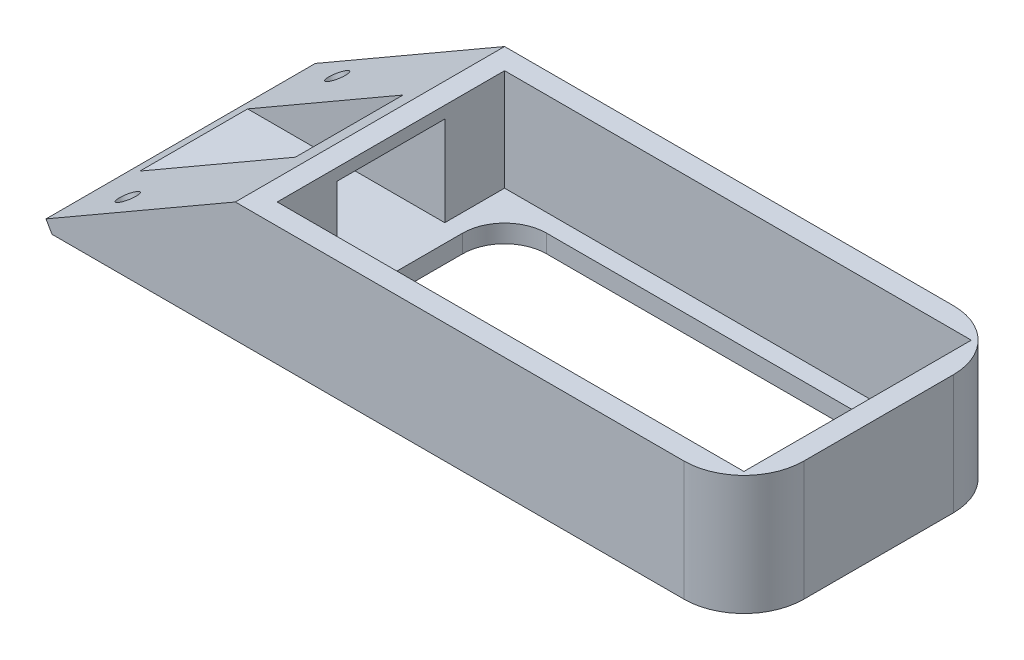
SolidWorks part; units mm, degrees
ref_plane "Front Plane" through (0, 0, 0) normal (0, 0, 1) x (1, 0, 0)
ref_plane "Top Plane" through (0, 0, 0) normal (0, 1, 0) x (1, 0, 0)
ref_plane "Right Plane" through (0, 0, 0) normal (1, 0, 0) x (0, 0, -1)
sketch "Sketch1" plane through (0, 0, 0) normal (0, 0, 1) x (1, 0, 0)
  line L0 (0, 0) -> (34.641, 20)
  line L1 (0, 0) -> (119.641, 0)
  line L2 (0, 0) -> (0, 20)
  line L3 (0, 20) -> (119.641, 20)
  line L4 (119.641, 0) -> (119.641, 20)
  line L5 (4, 0) -> (3, 1.7321)
  line L7 (34.641, 20) -> (34.641, 0) construction
  point P5 (5.8262, 0)
  point P10 (4.4285, 2.5568)
  dimension "D1" = 30
  dimension "D2" = 60
  dimension "D3" = 20
  dimension "D4" = 85
  dimension "D5" = 2
extrude "Boss-Extrude1" add sketch "Sketch1" along normal blind 45 contours L7 L0 L1 | L3 L7 L1 L4
sketch "Sketch2" plane through (0, 20, 0) normal (0, 1, 0) x (1, 0, 0)
  line L0 (116.141, -22.5) -> (119.641, -22.5) construction
  line L1 (38.141, -41.5) -> (116.141, -41.5)
  line L2 (38.141, -41.5) -> (38.141, -3.5)
  line L3 (38.141, -3.5) -> (116.141, -3.5)
  line L4 (116.141, -41.5) -> (116.141, -3.5)
  line L6 (119.641, -45) -> (119.641, 0) construction
  line L8 (77.141, -3.5) -> (77.141, 0) construction
  line L9 (34.641, 0) -> (119.641, 0) construction
  line L10 (38.141, -22.5) -> (34.641, -22.5) construction
  line L11 (34.641, -45) -> (34.641, 0) construction
  dimension "D1" = 78
  dimension "D2" = 38
extrude "Cut-Extrude1" cut sketch "Sketch2" against normal offset from surface (17 mm away) 3 up to face at (61.8205, 0, 22.5)
sketch "Sketch3" plane through (0, 3, 0) normal (0, 1, 0) x (1, 0, 0)
  line L1 (41.141, -38.5) -> (113.141, -38.5)
  line L2 (41.141, -38.5) -> (41.141, -6.5)
  line L3 (41.141, -6.5) -> (113.141, -6.5)
  line L4 (113.141, -38.5) -> (113.141, -6.5)
  line L7 (41.141, -6.5) -> (38.141, -3.5) construction
  line L8 (113.141, -38.5) -> (116.141, -41.5) construction
  dimension "D1" = 72
  dimension "D2" = 32
extrude "Cut-Extrude2" cut sketch "Sketch3" against normal up to next
fillet "Fillet1" radius 10 2 edges at (119.641, 10, 0) (119.641, 10, 45)
fillet "Fillet2" radius 7 4 edges at (41.141, 1.5, 6.5) (41.141, 1.5, 38.5) (113.141, 1.5, 6.5) (113.141, 1.5, 38.5)
sketch "Sketch4" plane through (38.141, 0, 0) normal (1, 0, 0) x (0, 0, -1)
  line L0 (-41.5, 3) -> (-3.5, 3) construction
  line L1 (-31.5, 3) -> (-13.5, 3)
  line L2 (-31.5, 3) -> (-31.5, 18)
  line L3 (-31.5, 18) -> (-13.5, 18)
  line L4 (-13.5, 3) -> (-13.5, 18)
  line L5 (-31.5, 18) -> (-41.5, 18) construction
  line L6 (-41.5, 3) -> (-41.5, 20) construction
  line L7 (-13.5, 18) -> (-3.5, 18) construction
  line L8 (-3.5, 3) -> (-3.5, 20) construction
  dimension "D1" = 18
  dimension "D2" = 15
extrude "Cut-Extrude3" cut sketch "Sketch4" against normal up to next
sketch "Sketch5" plane through (0, 0, 0) normal (-0.5, 0.866, 0) x (0.866, 0.5, 0)
  line L0 (13.4641, -5) -> (13.4641, -40) construction
  line L1 (3.4641, -45) -> (3.4641, 0) construction
  line L2 (13.4641, -5) -> (13.4641, 0) construction
  line L3 (3.4641, 0) -> (40, 0) construction
  line L4 (13.4641, -40) -> (13.4641, -45) construction
  line L5 (3.4641, -45) -> (40, -45) construction
  line L6 (13.4641, -5) -> (3.4641, -5) construction
  circle A0 centre (13.4641, -5) radius 1.6
  circle A1 centre (13.4641, -40) radius 1.6
  dimension "D1" = 3.2
  dimension "D2" = 35
  dimension "D3" = 10
extrude "Cut-Extrude4" cut sketch "Sketch5" against normal offset from surface (4.5403 mm away) 2 from offset 0
